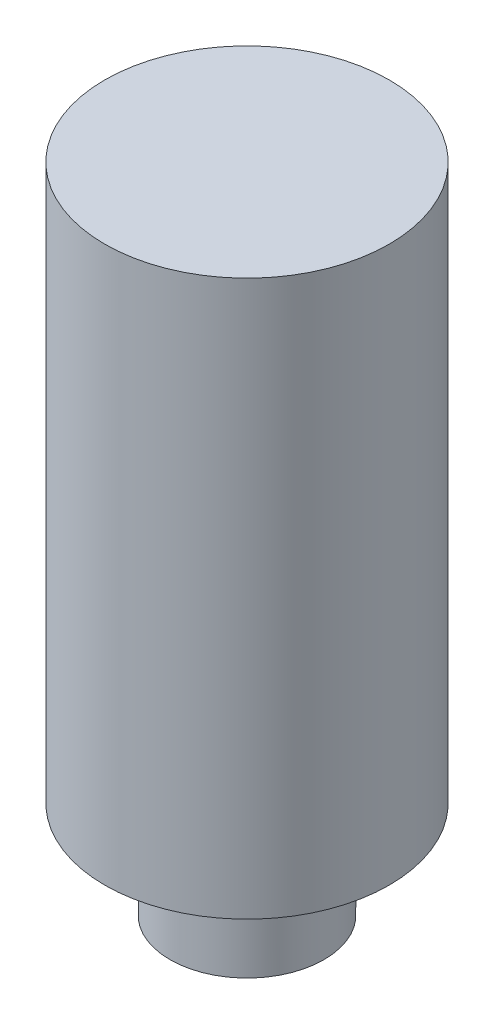
SolidWorks part; units mm, degrees
ref_plane "Alzado" through (0, 0, 0) normal (0, 0, 1) x (1, 0, 0)
ref_plane "Planta" through (0, 0, 0) normal (0, 1, 0) x (1, 0, 0)
ref_plane "Vista lateral" through (0, 0, 0) normal (1, 0, 0) x (0, 0, -1)
sketch "Croquis1" plane through (0, 0, 0) normal (0, 1, 0) x (1, 0, 0)
  circle A0 centre (0, 0) radius 10.25
  dimension "D1" = 20.5
extrude "Saliente-Extruir1" add sketch "Croquis1" along normal blind 40
sketch "Croquis2" plane through (0, 0, 0) normal (0, -1, 0) x (1, 0, 0)
  circle A0 centre (0, 0) radius 5.55
  circle A1 centre (0, 0) radius 2.45
  dimension "D1" = 11.1
  dimension "D2" = 4.9
extrude "Saliente-Extruir2" add sketch "Croquis2" along normal blind 7
